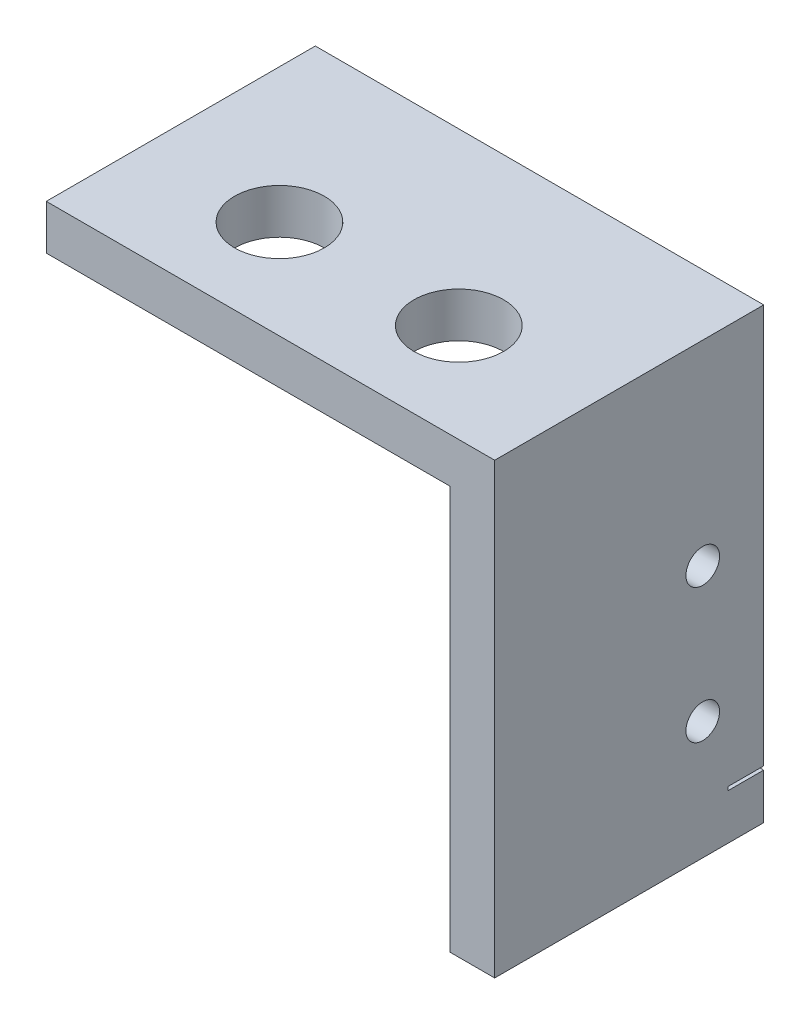
SolidWorks part; units mm, degrees
ref_plane "Front Plane" through (0, 0, 0) normal (0, 0, 1) x (1, 0, 0)
ref_plane "Top Plane" through (0, 0, 0) normal (0, 1, 0) x (1, 0, 0)
ref_plane "Right Plane" through (0, 0, 0) normal (1, 0, 0) x (0, 0, -1)
sketch "Sketch1" plane through (0, 0, 0) normal (0, 0, 1) x (1, 0, 0)
  line L1 (0, 0) -> (-31.75, 0)
  line L2 (0, 0) -> (0, 3.175)
  line L3 (0, 3.175) -> (-31.75, 3.175)
  line L4 (-31.75, 0) -> (-31.75, 3.175)
  line L5 (0, 0) -> (-3.175, 0)
  line L6 (0, 0) -> (0, -28.575)
  line L7 (0, -28.575) -> (-3.175, -28.575)
  line L8 (-3.175, 0) -> (-3.175, -28.575)
  dimension "D1" = 3.175
  dimension "D2" = 3.175
  dimension "D3" = 31.75
  dimension "D4" = 31.75
extrude "Boss-Extrude1" add sketch "Sketch1" along normal blind 19.05 contours L4 L1 L2 L3 | L1 L8 L7 L6
sketch "Sketch2" plane through (-3.175, 0, 0) normal (-1, 0, 0) x (0, 0, 1)
  line L0 (0, 0) -> (0, -28.575) construction
  line L1 (0, -28.575) -> (19.05, -28.575) construction
  line L2 (19.05, -28.575) -> (19.05, 0) construction
  line L3 (19.05, 0) -> (0, 0) construction
  line L4 (0, -10.668) -> (19.05, -10.668) construction
  line L5 (0, -20.193) -> (19.05, -20.193) construction
  line L6 (4.318, -10.668) -> (4.318, -20.193) construction
  line L8 (0, -25.0952) -> (2.54, -25.0952)
  line L9 (0, -25.0952) -> (0, -25.3492)
  line L10 (0, -25.3492) -> (2.54, -25.3492)
  line L11 (2.54, -25.0952) -> (2.54, -25.3492)
  circle A0 centre (4.318, -10.668) radius 1.1906
  circle A1 centre (4.318, -20.193) radius 1.1906
  dimension "D4" = 2.3813
  dimension "D5" = 2.3813
  dimension "D1" = 10.668
  dimension "D2" = 9.525
  dimension "D3" = 4.318
  dimension "D6" = 4.9022
  dimension "D7" = 5.1562
  dimension "D8" = 2.54
extrude "Switch Mount" cut sketch "Sketch2" against normal up to next
sketch "Sketch3" plane through (0, 0, 0) normal (0, -1, 0) x (1, 0, 0)
  line L0 (-3.175, 0) -> (-3.175, 19.05) construction
  line L1 (-3.175, 19.05) -> (-31.75, 19.05) construction
  line L2 (-31.75, 19.05) -> (-31.75, 0) construction
  line L3 (-31.75, 0) -> (-3.175, 0) construction
  line L4 (-3.175, 12.065) -> (-28.575, 12.065) construction
  circle A0 centre (-9.525, 12.065) radius 3.175
  circle A1 centre (-22.225, 12.065) radius 3.175
  dimension "D1" = 6.35
  dimension "D2" = 6.35
  dimension "D3" = 6.35
  dimension "D4" = 12.7
  dimension "D5" = 12.065
extrude "Bracket Mount" cut sketch "Sketch3" against normal up to next
